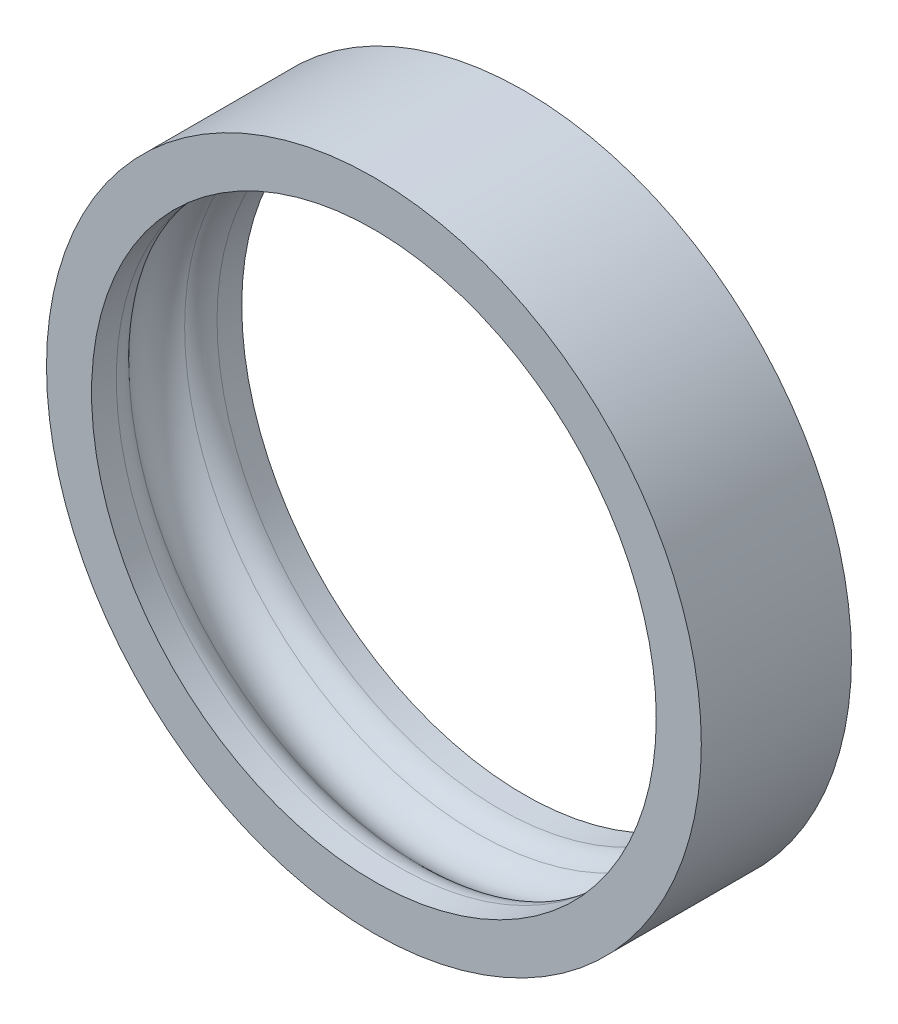
SolidWorks part; units mm, degrees
ref_plane "前视基准面" through (0, 0, 0) normal (0, 0, 1) x (1, 0, 0)
ref_plane "上视基准面" through (0, 0, 0) normal (0, 1, 0) x (1, 0, 0)
ref_plane "右视基准面" through (0, 0, 0) normal (1, 0, 0) x (0, 0, -1)
sketch "草图1" plane through (0, 0, 0) normal (0, 0, 1) x (1, 0, 0)
  circle A0 centre (0, 0) radius 9.4
  circle A1 centre (0, 0) radius 10.9
  dimension "D1" = 21.8
  dimension "D2" = 18.8
extrude "凸台-拉伸1" add sketch "草图1" along normal mid plane 5
sketch "草图3" plane through (0, 0, 0) normal (0, 1, 0) x (1, 0, 0)
  circle A0 centre (-8.9, 0) radius 1.25
  dimension "D1" = 2.5
  dimension "D2" = 8.9
revolve "切除-旋转1" cut sketch "草图3" angle 360 about axis through (0, 0, 2.5) along (0, 0, -1)
fillet "圆角1" radius 1 2 edges at (-9.4, 0, 1.1456) (9.4, 0, -1.1456)
equation "\"d\"= 21.8"
equation "\"D1@草图1\"=\"d\""
equation "\"d2\"= \"d\" - 3"
equation "\"D2@草图1\"=\"d2\""
equation "\"l1\"= \"d2\" / 2 - 0.5"
equation "\"D2@草图3\"=\"l1\""
